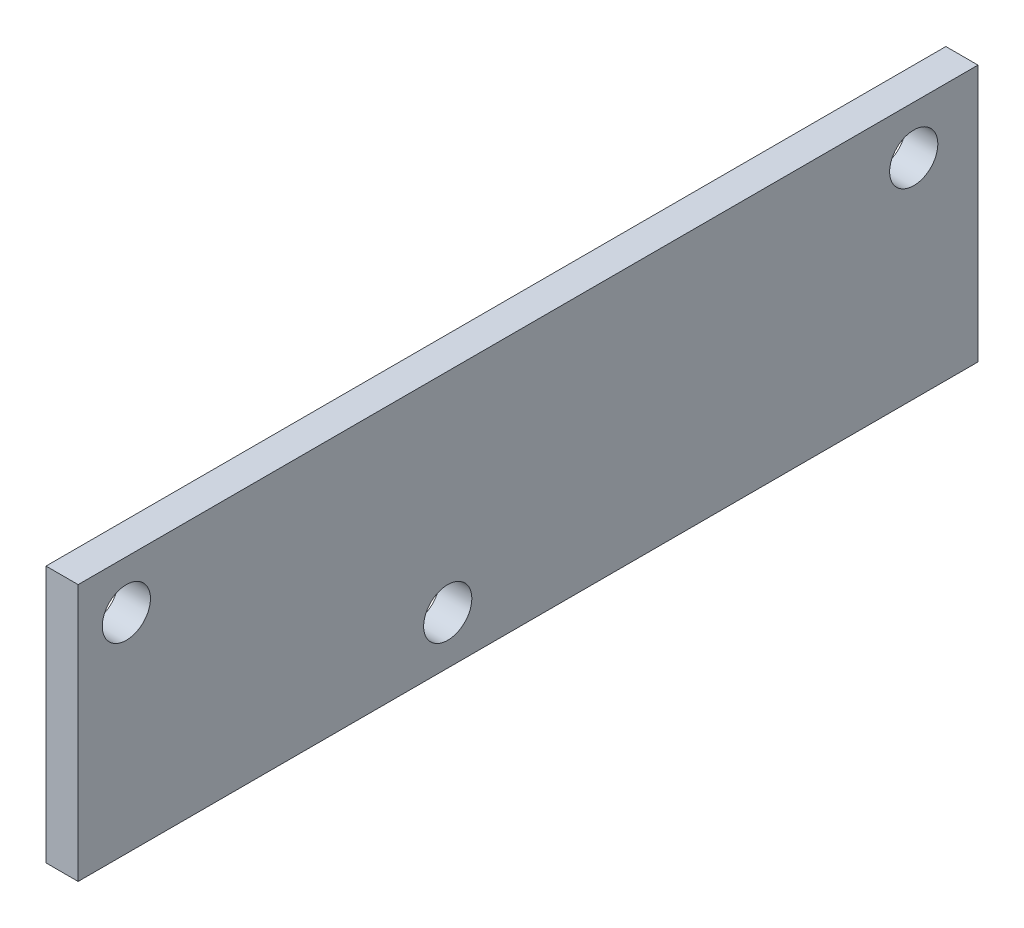
SolidWorks part; units mm, degrees
ref_plane "Front Plane" through (0, 0, 0) normal (0, 0, 1) x (1, 0, 0)
ref_plane "Top Plane" through (0, 0, 0) normal (0, 1, 0) x (1, 0, 0)
ref_plane "Right Plane" through (0, 0, 0) normal (1, 0, 0) x (0, 0, -1)
sketch "Sketch1" plane through (0, 0, 0) normal (1, 0, 0) x (0, 0, -1)
  line L1 (-177.8, 50.8) -> (177.8, 50.8)
  line L2 (-177.8, 50.8) -> (-177.8, -50.8)
  line L3 (-177.8, -50.8) -> (177.8, -50.8)
  line L4 (177.8, 50.8) -> (177.8, -50.8)
  line L5 (-177.8, 50.8) -> (177.8, -50.8) construction
  line L6 (-177.8, -50.8) -> (177.8, 50.8) construction
  point P0 (0, 0)
  dimension "D1" = 355.6
  dimension "D2" = 101.6
extrude "Boss-Extrude1" add sketch "Sketch1" along normal mid plane 12.7
sketch "Sketch2" plane through (6.35, 0, 0) normal (1, 0, 0) x (0, 0, -1)
  line L0 (177.8, 50.8) -> (-177.8, 50.8) construction
  line L1 (-177.8, 50.8) -> (-177.8, -50.8) construction
  line L2 (177.8, -50.8) -> (177.8, 50.8) construction
  line L3 (-177.8, -50.8) -> (177.8, -50.8) construction
  circle A0 centre (-158.75, 31.75) radius 9.525
  circle A1 centre (-31.75, -31.75) radius 9.525
  circle A2 centre (152.4, 31.75) radius 9.525
  dimension "D1" = 19.05
  dimension "D2" = 19.05
  dimension "D3" = 127
  dimension "D4" = 25.4
  dimension "D5" = 19.05
  dimension "D6" = 19.05
  dimension "D7" = 19.05
extrude "Cut-Extrude1" cut sketch "Sketch2" against normal up to next
